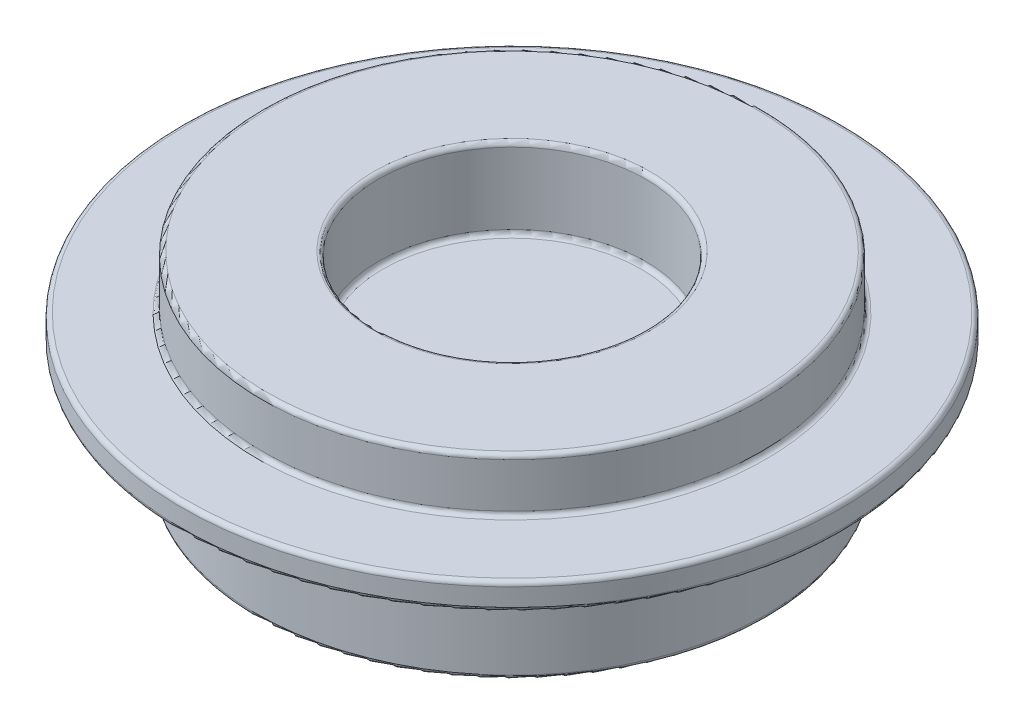
SolidWorks part; units mm, degrees
ref_plane "Front Plane" through (0, 0, 0) normal (0, 0, 1) x (1, 0, 0)
ref_plane "Top Plane" through (0, 0, 0) normal (0, 1, 0) x (1, 0, 0)
ref_plane "Right Plane" through (0, 0, 0) normal (1, 0, 0) x (0, 0, -1)
sketch "Sketch1" plane through (0, 0, 0) normal (0, 0, 1) x (1, 0, 0)
  line L0 (0, 17.9687) -> (0, -17.9687) construction
  line L1 (0, 0) -> (0, 6.25)
  line L2 (0, 6.25) -> (-7.5, 6.25)
  line L3 (-7.5, 6.25) -> (-7.5, 10.75)
  line L4 (-7.5, 10.75) -> (-14, 10.75)
  line L5 (-14, 10.75) -> (-14, 7.75)
  line L6 (-14, 7.75) -> (-18.5, 7.75)
  line L7 (-18.5, 7.75) -> (-18.5, 6.25)
  line L8 (-18.5, 6.25) -> (-14.3125, 6.25)
  line L9 (-14.3125, 6.25) -> (-14.3125, 0)
  line L10 (-14.3125, 0) -> (0, 0)
  point P4 (0, 0)
  dimension "D1" = 7.5
  dimension "D2" = 6.5
  dimension "D3" = 4.5
  dimension "D4" = 3
  dimension "D5" = 1.5
  dimension "D6" = 6.25
  dimension "D7" = 14.3125
  dimension "D8" = 6.25
revolve "Revolve1" add sketch "Sketch1" angle 360 about L0
fillet "Fillet1" radius 0.25 8 edges at (-18.5, 7.75, 0) (-18.5, 6.25, 0) (-7.5, 6.25, 0) (-7.5, 10.75, 0) (-14, 10.75, 0) (-14.3125, 6.25, 0) (-14, 7.75, 0) (-14.3125, 0, 0)
